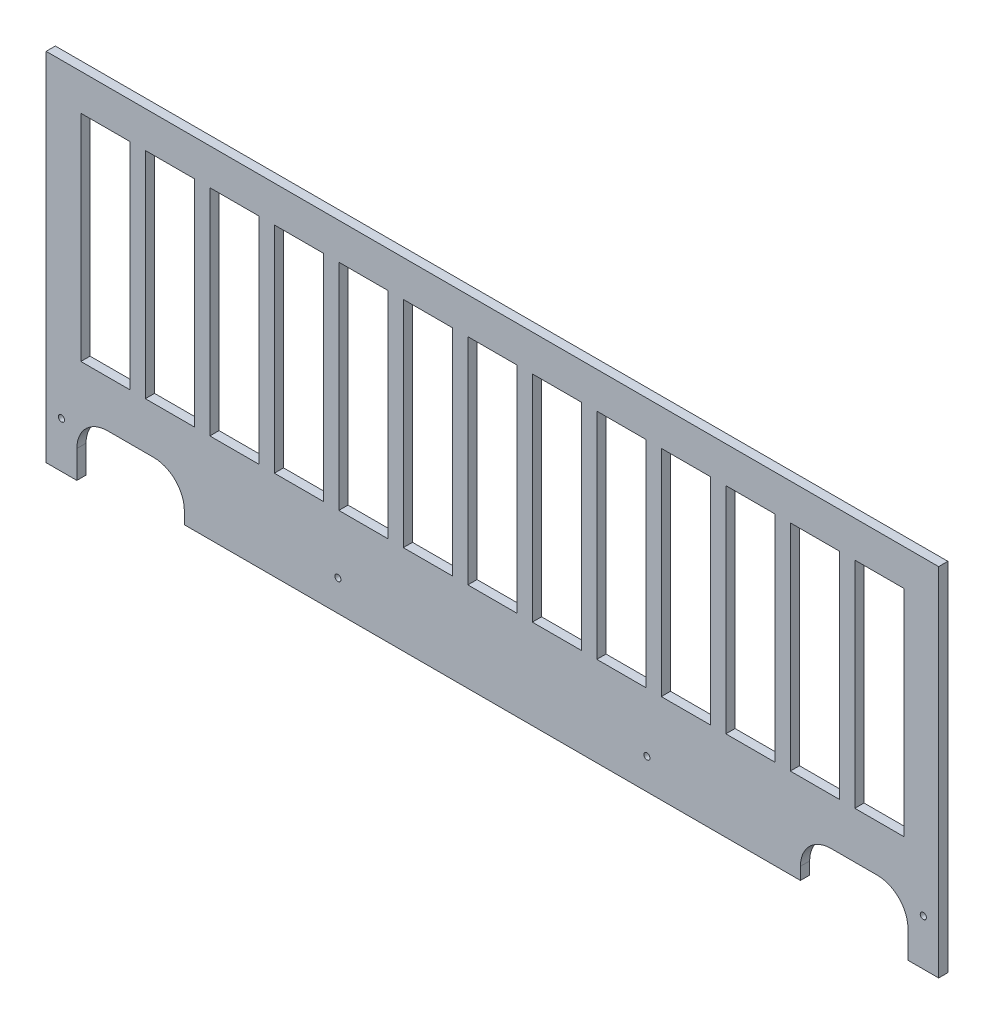
SolidWorks part; units mm, degrees
ref_plane "Plane1" through (0, 0, 0) normal (0, 0, 1) x (1, 0, 0)
ref_plane "Plane2" through (0, 0, 0) normal (0, 1, 0) x (1, 0, 0)
ref_plane "Plane3" through (0, 0, 0) normal (1, 0, 0) x (0, 0, -1)
sketch "Esquisse5" plane through (0, 0, 0) normal (0, 0, 1) x (1, 0, 0)
  line L7 (-3.9285, 116) -> (286.6703, 116)
  line L8 (-3.9285, 116) -> (-3.9285, 0)
  line L9 (16.07, 19.0001) -> (31.07, 19.0001)
  line L10 (286.6703, 116) -> (286.6703, 0)
  line L15 (28.373, 104.2) -> (44.373, 104.2)
  line L16 (7.373, 104.2) -> (23.373, 104.2)
  line L17 (7.373, 104.2) -> (7.373, 34.2)
  line L18 (7.373, 34.2) -> (23.373, 34.2)
  line L19 (23.373, 104.2) -> (23.373, 34.2)
  line L20 (28.373, 104.2) -> (28.373, 34.2)
  line L21 (28.373, 34.2) -> (44.373, 34.2)
  line L22 (44.373, 104.2) -> (44.373, 34.2)
  line L23 (49.373, 104.2) -> (65.373, 104.2)
  line L24 (49.373, 104.2) -> (49.373, 34.2)
  line L25 (49.373, 34.2) -> (65.373, 34.2)
  line L26 (65.373, 104.2) -> (65.373, 34.2)
  line L27 (70.373, 104.2) -> (86.373, 104.2)
  line L28 (70.373, 104.2) -> (70.373, 34.2)
  line L29 (70.373, 34.2) -> (86.373, 34.2)
  line L30 (86.373, 104.2) -> (86.373, 34.2)
  line L31 (91.373, 104.2) -> (107.373, 104.2)
  line L32 (91.373, 104.2) -> (91.373, 34.2)
  line L33 (91.373, 34.2) -> (107.373, 34.2)
  line L34 (107.373, 104.2) -> (107.373, 34.2)
  line L35 (112.373, 104.2) -> (128.373, 104.2)
  line L36 (112.373, 104.2) -> (112.373, 34.2)
  line L37 (112.373, 34.2) -> (128.373, 34.2)
  line L38 (128.373, 104.2) -> (128.373, 34.2)
  line L39 (133.373, 104.2) -> (149.373, 104.2)
  line L40 (133.373, 104.2) -> (133.373, 34.2)
  line L41 (133.373, 34.2) -> (149.373, 34.2)
  line L42 (149.373, 104.2) -> (149.373, 34.2)
  line L43 (154.373, 104.2) -> (170.373, 104.2)
  line L44 (154.373, 104.2) -> (154.373, 34.2)
  line L45 (154.373, 34.2) -> (170.373, 34.2)
  line L46 (170.373, 104.2) -> (170.373, 34.2)
  line L47 (175.373, 104.2) -> (191.373, 104.2)
  line L48 (175.373, 104.2) -> (175.373, 34.2)
  line L49 (175.373, 34.2) -> (191.373, 34.2)
  line L50 (191.373, 104.2) -> (191.373, 34.2)
  line L51 (196.373, 104.2) -> (212.373, 104.2)
  line L52 (196.373, 104.2) -> (196.373, 34.2)
  line L53 (196.373, 34.2) -> (212.373, 34.2)
  line L54 (212.373, 104.2) -> (212.373, 34.2)
  line L55 (217.373, 104.2) -> (233.373, 104.2)
  line L56 (217.373, 104.2) -> (217.373, 34.2)
  line L57 (217.373, 34.2) -> (233.373, 34.2)
  line L58 (233.373, 104.2) -> (233.373, 34.2)
  line L59 (238.373, 104.2) -> (254.373, 104.2)
  line L60 (238.373, 104.2) -> (238.373, 34.2)
  line L61 (238.373, 34.2) -> (254.373, 34.2)
  line L62 (254.373, 104.2) -> (254.373, 34.2)
  line L63 (259.373, 104.2) -> (275.373, 104.2)
  line L64 (259.373, 104.2) -> (259.373, 34.2)
  line L65 (259.373, 34.2) -> (275.373, 34.2)
  line L66 (275.373, 104.2) -> (275.373, 34.2)
  line L71 (-3.9285, 0) -> (6.07, 0)
  line L72 (6.07, 0) -> (6.07, 9.0001)
  line L73 (41.07, 9.0001) -> (41.07, 5.0001)
  line L74 (251.6703, 19.0001) -> (266.6703, 19.0001)
  line L75 (241.6703, 9.0001) -> (241.6703, 5.0001)
  line L77 (276.6703, 0) -> (276.6703, 9)
  line L78 (286.6703, 0) -> (276.6703, 0)
  line L79 (41.07, 5.0001) -> (241.6703, 5.0001)
  circle A0 centre (191.6703, 15) radius 1
  arc A1 (16.07, 19.0001) -> (6.07, 9.0001) centre (16.07, 9.0001) ccw
  arc A3 (41.07, 9.0001) -> (31.07, 19.0001) centre (31.07, 9.0001) ccw
  arc A5 (241.6703, 9.0001) -> (251.6703, 19.0001) centre (251.6703, 9.0001) cw
  arc A6 (266.6703, 19.0001) -> (276.6703, 9) centre (266.6703, 9.0001) cw
  circle A7 centre (1.0715, 15) radius 1
  circle A8 centre (91.0715, 15) radius 1
  circle A9 centre (281.6703, 15) radius 1
  point P99 (6.07, 19.0001)
  point P102 (41.07, 19.0001)
  dimension "D3" = 290.5988
  dimension "D12" = 10
  dimension "D15" = 5
  dimension "D16" = 90
  dimension "D17" = 2
  dimension "D19" = 10
  dimension "D10" = 15
  dimension "D4" = 3.9285
  dimension "D5" = 9.9985
  dimension "D6" = 14
  dimension "D7" = 19.9985
  dimension "D8" = 35
  dimension "D9" = 35
  dimension "D11" = 116
  dimension "D13" = 5
  dimension "D14" = 90
  dimension "D18" = 15
  dimension "D20" = 200.6003
  dimension "D21" = 15
  dimension "D23" = 11.3015
  dimension "D24" = 16
  dimension "D25" = 5
  dimension "D26" = 70
  dimension "D27" = 11.8
  dimension "D28" = 5.0001
  dimension "D29" = 9
  dimension "D22" = 13
extrude "Extrusion1" add sketch "Esquisse5" along normal blind 3
